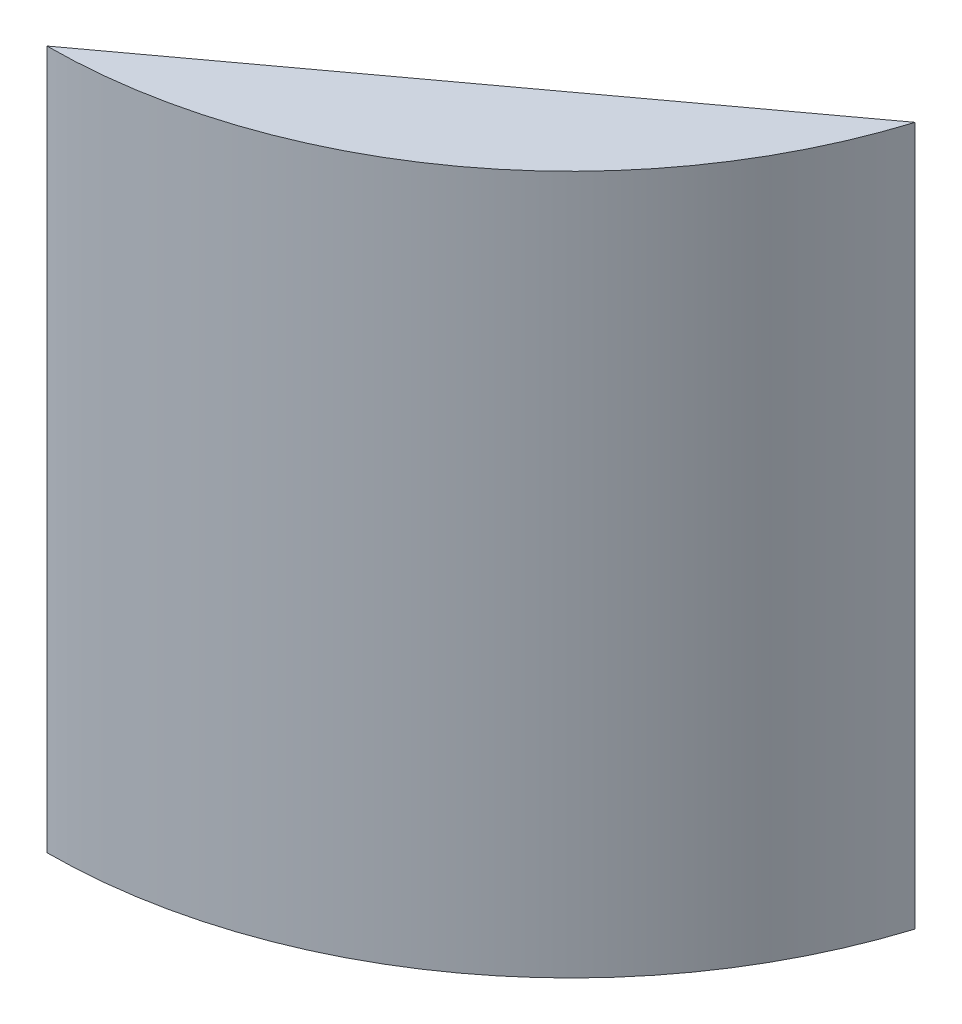
SolidWorks part; units mm, degrees
ref_plane "Front Plane" through (0, 0, 0) normal (0, 0, 1) x (1, 0, 0)
ref_plane "Top Plane" through (0, 0, 0) normal (0, 1, 0) x (1, 0, 0)
ref_plane "Right Plane" through (0, 0, 0) normal (1, 0, 0) x (0, 0, -1)
sketch "Sketch1" plane through (0, 0, 0) normal (0, 1, 0) x (1, 0, 0)
  circle A0 centre (0, 0) radius 85.725
extrude "Boss-Extrude1" add sketch "Sketch1" along normal blind 114.3
sketch "Sketch2" plane through (0, 114.3, 0) normal (0, 1, 0) x (1, 0, 0)
  line L0 (0, -85.725) -> (81.839, -25.5176)
  line L1 (81.839, -25.5176) -> (151.3047, 75.0629)
  line L2 (151.3047, 75.0629) -> (-38.5139, 115.9348)
  line L3 (-38.5139, 115.9348) -> (-149.3397, 18.864)
  line L4 (-149.3397, 18.864) -> (-68.7749, -104.5378)
  line L5 (-68.7749, -104.5378) -> (0, -85.725)
  circle A0 centre (0, 0) radius 85.725 construction
extrude "Cut-Extrude1" cut sketch "Sketch2" against normal blind 152.4
sketch "Sketch3" plane through (40.9195, 0, 55.6213) normal (-0.5926, 0, -0.8055) x (-0.8055, 0, 0.5926)
  line L0 (-50.8, 0) -> (-50.8, 114.3) construction
  line L1 (50.8, 0) -> (-50.8, 0) construction
  circle A0 centre (-36.83, 95.758) radius 2.7781
  circle A1 centre (11.176, 95.758) radius 2.7781
  circle A2 centre (-36.83, 70.358) radius 2.7781
  circle A3 centre (11.176, 70.358) radius 2.7781
  circle A4 centre (-36.83, 51.308) radius 2.7781
  circle A5 centre (6.096, 51.308) radius 2.7781
  circle A6 centre (-36.83, 30.48) radius 2.7781
  circle A7 centre (6.096, 30.48) radius 2.7781
  dimension "D2" = 13.97
  dimension "D7" = 19.05
  dimension "D3" = 48.006
  dimension "D4" = 25.4
  dimension "D5" = 48.006
  dimension "D6" = 25.4
  dimension "D8" = 42.926
  dimension "D9" = 20.828
  dimension "D10" = 20.828
  dimension "D11" = 42.926
  dimension "D12" = 30.48
extrude "Cut-Extrude2" cut sketch "Sketch3" against normal blind 3.175
sketch "Sketch4" plane through (0, 0, 0) normal (0, -1, 0) x (-1, 0, 0)
  line L0 (-40.9195, -55.6213) -> (-50.8, -69.0517) construction
  line L1 (0, -85.725) -> (-81.839, -25.5176) construction
  arc A0 (-81.839, -25.5176) -> (0, -85.725) centre (0, 0) ccw construction
  circle A1 centre (-45.8598, -62.3365) radius 5.588
  dimension "D1" = 11.176
extrude "Cut-Extrude3" cut sketch "Sketch4" against normal blind 6.096
